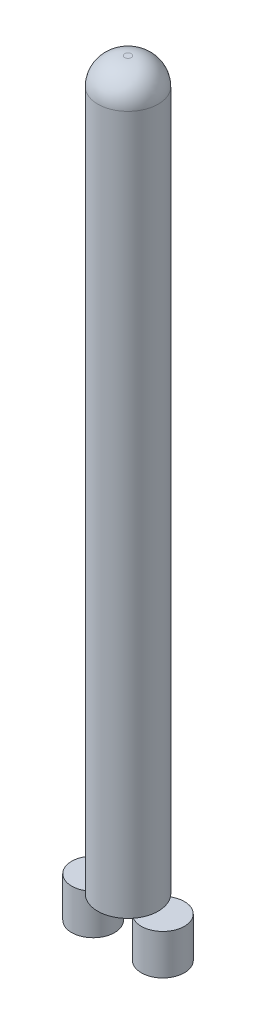
SolidWorks part; units mm, degrees
ref_plane "Front Plane" through (0, 0, 0) normal (0, 0, 1) x (1, 0, 0)
ref_plane "Top Plane" through (0, 0, 0) normal (0, 1, 0) x (1, 0, 0)
ref_plane "Right Plane" through (0, 0, 0) normal (1, 0, 0) x (0, 0, -1)
sketch "Sketch1" plane through (0, 0, 0) normal (0, 1, 0) x (1, 0, 0)
  circle A0 centre (0, 0) radius 45
  circle A1 centre (0, 0) radius 42
  dimension "D1" = 90
  dimension "D2" = 3
extrude "Boss-Extrude1" add sketch "Sketch1" along normal blind 1000
sketch "Sketch2" plane through (0, 1000, 0) normal (0, 1, 0) x (1, 0, 0)
  circle A0 centre (0, 0) radius 45
extrude "Boss-Extrude2" add sketch "Sketch2" along normal blind 80
fillet "Fillet1" radius 40 1 edges at (0, 1080, 45)
sketch "Sketch3" plane through (0, 0, 0) normal (0, 1, 0) x (1, 0, 0)
  line L0 (0, 0) -> (51.8508, 0) construction
  line L1 (0, 0) -> (0, 54.5226) construction
  circle A0 centre (51.8508, 0) radius 32
  circle A1 centre (-51.8508, 0) radius 32
  point P6 (0, 0)
  point P7 (51.8508, 0)
  dimension "D1" = 64
extrude "Boss-Extrude3" add sketch "Sketch3" against normal blind 60 separate body
